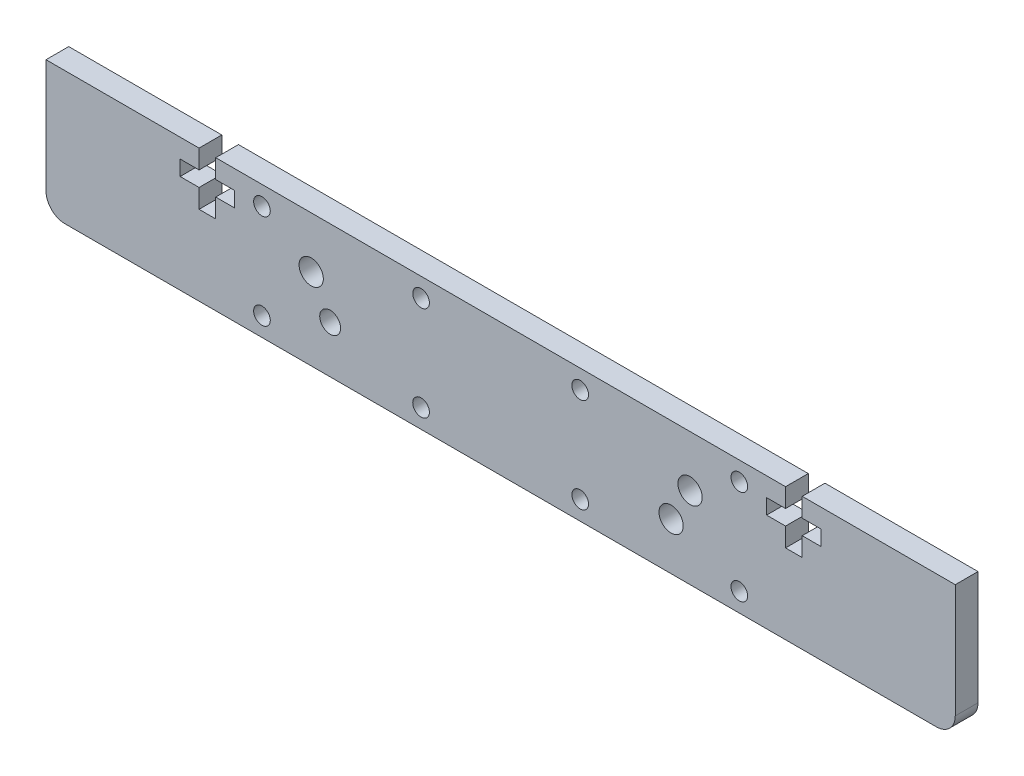
SolidWorks part; units mm, degrees
material "Acrylic (Medium-high impact)"
ref_plane "Front Plane" through (0, 0, 0) normal (0, 0, 1) x (1, 0, 0)
ref_plane "Top Plane" through (0, 0, 0) normal (0, 1, 0) x (1, 0, 0)
ref_plane "Right Plane" through (0, 0, 0) normal (1, 0, 0) x (0, 0, -1)
sketch "Sketch1" plane through (0, 0, 0) normal (0, 0, 1) x (1, 0, 0)
  line L0 (-60, 0) -> (60, 0) construction
  line L1 (-60, -8.75) -> (60, -8.75)
  line L2 (-60, -8.75) -> (-60, 8.75)
  line L3 (-60, 8.75) -> (60, 8.75) construction
  line L4 (60, -8.75) -> (60, 8.75)
  line L5 (-60, -8.75) -> (60, 8.75) construction
  line L6 (-60, 8.75) -> (60, -8.75) construction
  line L19 (0, 8.75) -> (0, -8.75) construction
  line L47 (-37.6, 8.75) -> (-37.6, 6.25)
  line L48 (-37.6, 6.25) -> (-35.1, 6.25)
  line L49 (-35.1, 6.25) -> (-35.1, 4.25)
  line L50 (-35.1, 4.25) -> (-37.6, 4.25)
  line L51 (-37.6, 4.25) -> (-37.6, 1.75)
  line L52 (-37.6, 1.75) -> (-39.8, 1.75)
  line L70 (-39.8, 1.75) -> (-39.8, 4.25)
  line L71 (-39.8, 4.25) -> (-42.3, 4.25)
  line L72 (-42.3, 4.25) -> (-42.3, 6.25)
  line L73 (-42.3, 6.25) -> (-39.8, 6.25)
  line L74 (-39.8, 6.25) -> (-39.8, 8.75)
  line L75 (39.8, 6.25) -> (39.8, 8.75)
  line L76 (42.3, 6.25) -> (39.8, 6.25)
  line L77 (42.3, 4.25) -> (42.3, 6.25)
  line L78 (39.8, 4.25) -> (42.3, 4.25)
  line L79 (39.8, 1.75) -> (39.8, 4.25)
  line L80 (37.6, 1.75) -> (39.8, 1.75)
  line L81 (37.6, 4.25) -> (37.6, 1.75)
  line L82 (35.1, 4.25) -> (37.6, 4.25)
  line L83 (35.1, 6.25) -> (35.1, 4.25)
  line L84 (37.6, 6.25) -> (35.1, 6.25)
  line L85 (37.6, 8.75) -> (37.6, 6.25)
  line L86 (-60, 8.75) -> (-39.8, 8.75)
  line L87 (-37.6, 8.75) -> (37.6, 8.75)
  line L88 (39.8, 8.75) -> (60, 8.75)
  circle A5 centre (-10.5, 6.25) radius 1.1
  circle A9 centre (-10.5, -6.25) radius 1.1
  circle A12 centre (10.5, -6.25) radius 1.1
  circle A13 centre (10.5, 6.25) radius 1.1
  circle A14 centre (-31.5, 6.25) radius 1.1
  circle A16 centre (-31.5, -6.25) radius 1.1
  circle A17 centre (31.5, -6.25) radius 1.1
  circle A18 centre (31.5, 6.25) radius 1.1
  circle A19 centre (25, 2) radius 1.6
  circle A20 centre (-25, 2) radius 1.6
  circle A21 centre (22.5, -2.5) radius 1.6
  circle A22 centre (-22.5, -2.5) radius 1.375
  point P0 (0, 0)
  dimension "D3" = 2.2
  dimension "D7" = 3.2
  dimension "D12" = 2.2
  dimension "D4" = 50
  dimension "D8" = 45
  dimension "D9" = 3.2
  dimension "D10" = 2.75
  dimension "D1" = 120
  dimension "D2" = 17.5
  dimension "D5" = 10.5
  dimension "D6" = 6.25
  dimension "D11" = 21
  dimension "D13" = 2.2
  dimension "D14" = 2.5
  dimension "D15" = 2
  dimension "D16" = 2.5
  dimension "D17" = 35.1
  dimension "D18" = 1.75
  dimension "D19" = 5
  dimension "D20" = 2
extrude "Boss-Extrude1" add sketch "Sketch1" along normal blind 3
fillet "Fillet1" radius 2.5 2 edges at (-60, -8.75, 1.5) (60, -8.75, 1.5)
